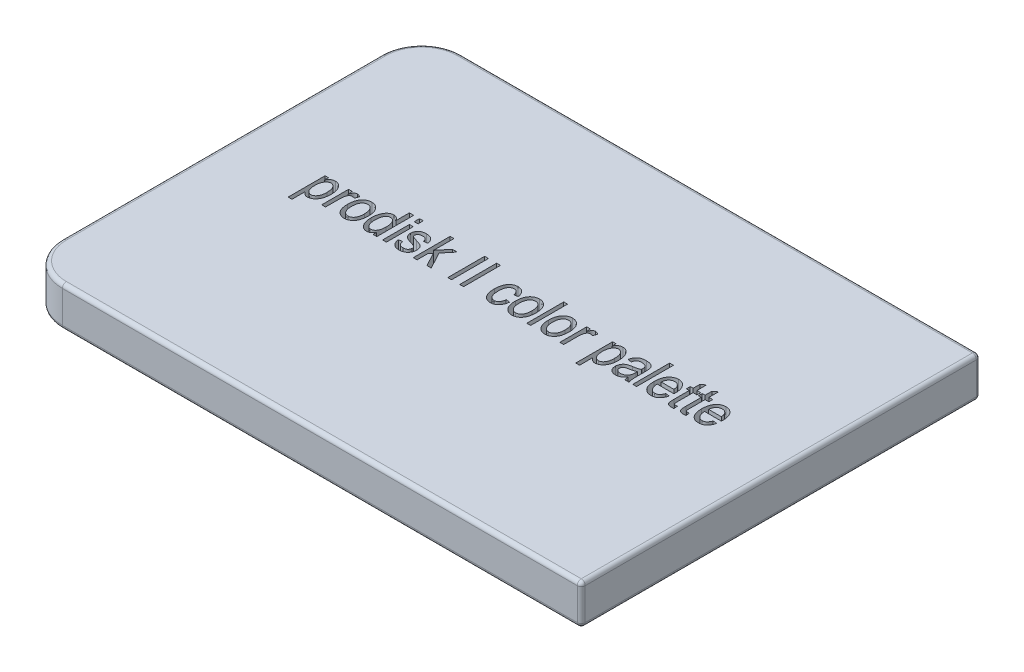
SolidWorks part; units mm, degrees
ref_plane "Front Plane" through (0, 0, 0) normal (0, 0, 1) x (1, 0, 0)
ref_plane "Top Plane" through (0, 0, 0) normal (0, 1, 0) x (1, 0, 0)
ref_plane "Right Plane" through (0, 0, 0) normal (1, 0, 0) x (0, 0, -1)
sketch "Sketch1" plane through (0, 0, 0) normal (0, 1, 0) x (1, 0, 0)
  line L1 (-55.473, 0) -> (84.527, 0)
  line L2 (-55.473, 0) -> (-55.473, -100)
  line L3 (-55.473, -100) -> (84.527, -100)
  line L4 (84.527, 0) -> (84.527, -100)
  dimension "D1" = 100
  dimension "D2" = 140
extrude "Boss-Extrude1" add sketch "Sketch1" along normal blind 10
fillet "Fillet1" radius 10 1 edges at (-55.473, 5, 0)
fillet "Fillet2" radius 10 1 edges at (-55.473, 5, 100)
fillet "Fillet3" radius 1 14 edges at (84.527, 0, 50) (19.527, 0, 0) (-52.544, 0, 2.9289) (-55.473, 0, 50) (-52.544, 0, 97.0711) (19.527, 0, 100) (-52.544, 10, 2.9289) (19.527, 10, 0) (84.527, 10, 50) (19.527, 10, 100) (-52.544, 10, 97.0711) (-55.473, 10, 50) (84.527, 5, 0) (84.527, 5, 100)
sketch "Sketch2" plane through (0, 0, 0) normal (0, 1, 0) x (1, 0, 0)
  line L0 (-46.746, -50.3677) -> (77.2507, -50.3677) construction
  text T0 "prodisk II color palette" font "Arial Narrow" height in points 36
extrude "Cut-Extrude1" cut sketch "Sketch2" against normal through all and the other way through all
